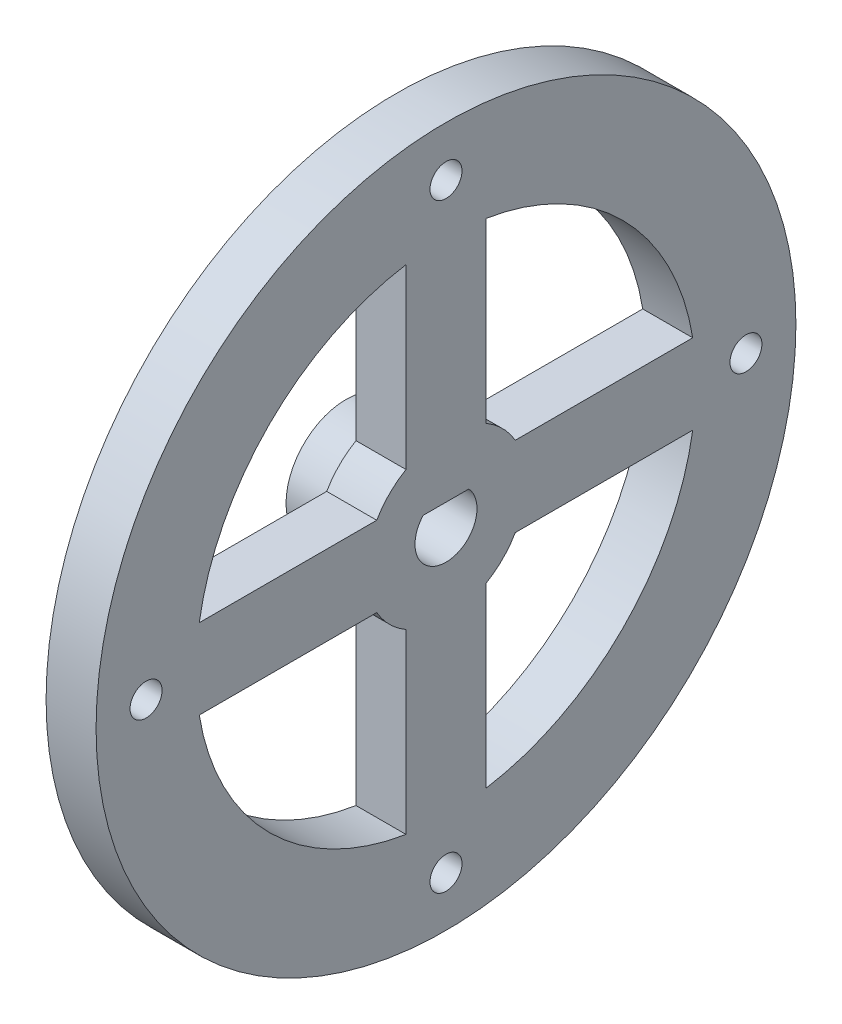
SolidWorks part; units mm, degrees
material "PLA (White)"
ref_plane "Front Plane" through (0, 0, 0) normal (0, 0, 1) x (1, 0, 0)
ref_plane "Top Plane" through (0, 0, 0) normal (0, 1, 0) x (1, 0, 0)
ref_plane "Right Plane" through (0, 0, 0) normal (1, 0, 0) x (0, 0, -1)
sketch "Sketch1" plane through (0, 0, 0) normal (1, 0, 0) x (0, 0, -1)
  line L0 (0, 0) -> (0, 50000) construction
  line L1 (4, 6.9282) -> (4, 24.6779)
  line L2 (-4, 24.6779) -> (-4, 6.9282)
  line L3 (-24.6779, -4) -> (-6.9282, -4)
  line L4 (-6.9282, 4) -> (-24.6779, 4)
  line L5 (4, -24.6779) -> (4, -6.9282)
  line L6 (-4, -6.9282) -> (-4, -24.6779)
  line L7 (24.6779, 4) -> (6.9282, 4)
  line L8 (6.9282, -4) -> (24.6779, -4)
  line L9 (-2.2804, 2.1) -> (2.2804, 2.1)
  circle A0 centre (0, 0) radius 35
  arc A1 (-2.2804, 2.1) -> (2.2804, 2.1) centre (0, 0) ccw
  arc A2 (-6.9282, -4) -> (-4, -6.9282) centre (0, 0) ccw
  arc A3 (-24.6779, -4) -> (-4, -24.6779) centre (0, 0) ccw
  arc A4 (-4, 6.9282) -> (-6.9282, 4) centre (0, 0) ccw
  arc A5 (24.6779, 4) -> (4, 24.6779) centre (0, 0) ccw
  arc A6 (4, -24.6779) -> (24.6779, -4) centre (0, 0) ccw
  arc A7 (4, -6.9282) -> (6.9282, -4) centre (0, 0) ccw
  arc A8 (6.9282, 4) -> (4, 6.9282) centre (0, 0) ccw
  arc A9 (-24.6779, 4) -> (-4, 24.6779) centre (0, 0) cw
  point P27 (0, 0)
  dimension "D1" = 70
  dimension "D2" = 6.2
  dimension "D5" = 16
  dimension "D6" = 50
  dimension "D3" = 8
  dimension "D7" = 2.1
  dimension "D4" = 4
extrude "Boss-Extrude1" add sketch "Sketch1" along normal blind 5
sketch "Sketch2" plane through (0, 0, 0) normal (-1, 0, 0) x (0, 0, 1)
  circle A0 centre (0, 0) radius 30 construction
  circle A1 centre (0, 30) radius 1.6
  circle A2 centre (30, 0) radius 1.6
  circle A3 centre (0, -30) radius 1.6
  circle A4 centre (-30, 0) radius 1.6
  point P14 (0, 0)
  dimension "D1" = 60
  dimension "D2" = 3.2
  dimension "D3" = 4
extrude "Cut-Extrude1" cut sketch "Sketch2" against normal through all
sketch "Sketch3" plane through (0, 0, 0) normal (-1, 0, 0) x (0, 0, 1)
  line L0 (-2.2804, 2.1) -> (2.2804, 2.1) construction
  line L1 (-2.2804, 2.1) -> (2.2804, 2.1)
  circle A2 centre (0, 0) radius 6
  arc A3 (-2.2804, 2.1) -> (2.2804, 2.1) centre (0, 0) ccw construction
  arc A4 (-2.2804, 2.1) -> (2.2804, 2.1) centre (0, 0) ccw
  dimension "D1" = 12
extrude "Boss-Extrude2" add sketch "Sketch3" along normal blind 5
sketch "Sketch6" plane through (0, 0, 0) normal (-1, 0, 0) x (0, 0, 1)
  circle A0 centre (0, 30) radius 4
  circle A1 centre (30, 0) radius 4
  circle A2 centre (0, -30) radius 4
  circle A3 centre (-30, 0) radius 4
  point P12 (0, 0)
  dimension "D1" = 8
  dimension "D2" = 4
extrude "Cut-Extrude2" cut sketch "Sketch6" against normal blind 2
